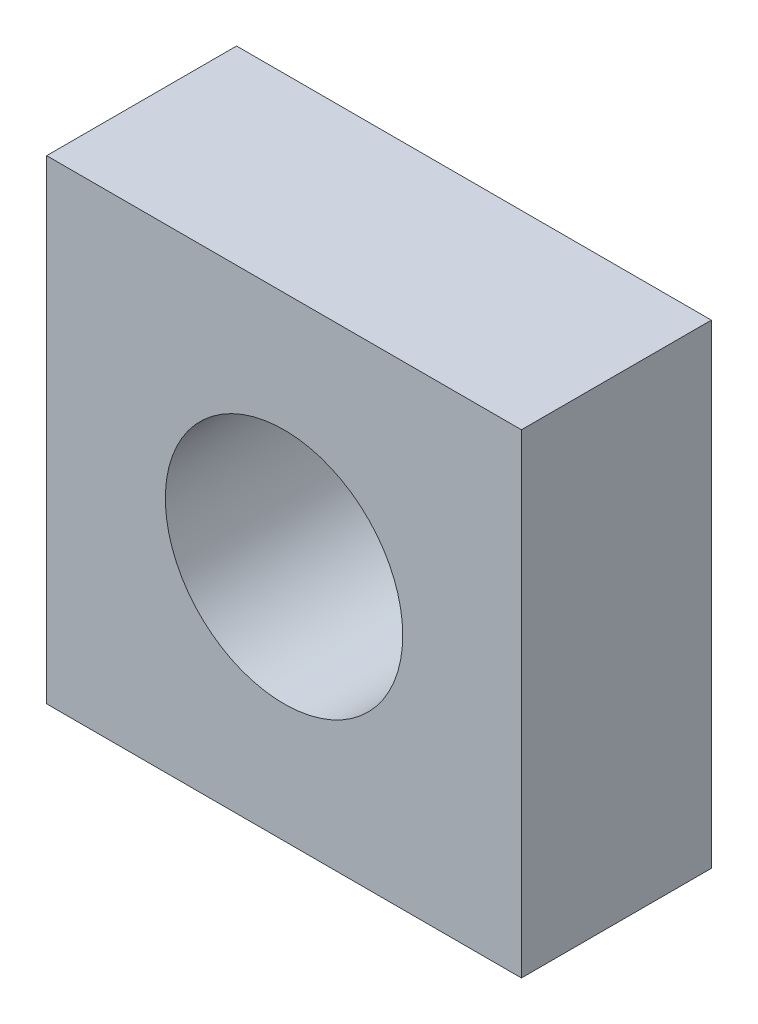
SolidWorks part; units mm, degrees
ref_plane "Front Plane" through (0, 0, 0) normal (0, 0, 1) x (1, 0, 0)
ref_plane "Top Plane" through (0, 0, 0) normal (0, 1, 0) x (1, 0, 0)
ref_plane "Right Plane" through (0, 0, 0) normal (1, 0, 0) x (0, 0, -1)
sketch "Sketch2" plane through (0, 0, 0) normal (0, 0, 1) x (1, 0, 0)
  line L1 (-5, 5) -> (5, 5)
  line L2 (-5, 5) -> (-5, -5)
  line L3 (-5, -5) -> (5, -5)
  line L4 (5, 5) -> (5, -5)
  line L5 (-5, 5) -> (5, -5) construction
  line L6 (-5, -5) -> (5, 5) construction
  point P0 (0, 0)
  dimension "D1" = 10
  dimension "D2" = 10
extrude "Boss-Extrude1" add sketch "Sketch2" along normal blind 4
sketch "Sketch3" plane through (0, 0, 4) normal (0, 0, 1) x (1, 0, 0)
  circle A0 centre (0, 0) radius 2.5
  dimension "D1" = 5
extrude "Cut-Extrude1" cut sketch "Sketch3" against normal through all
